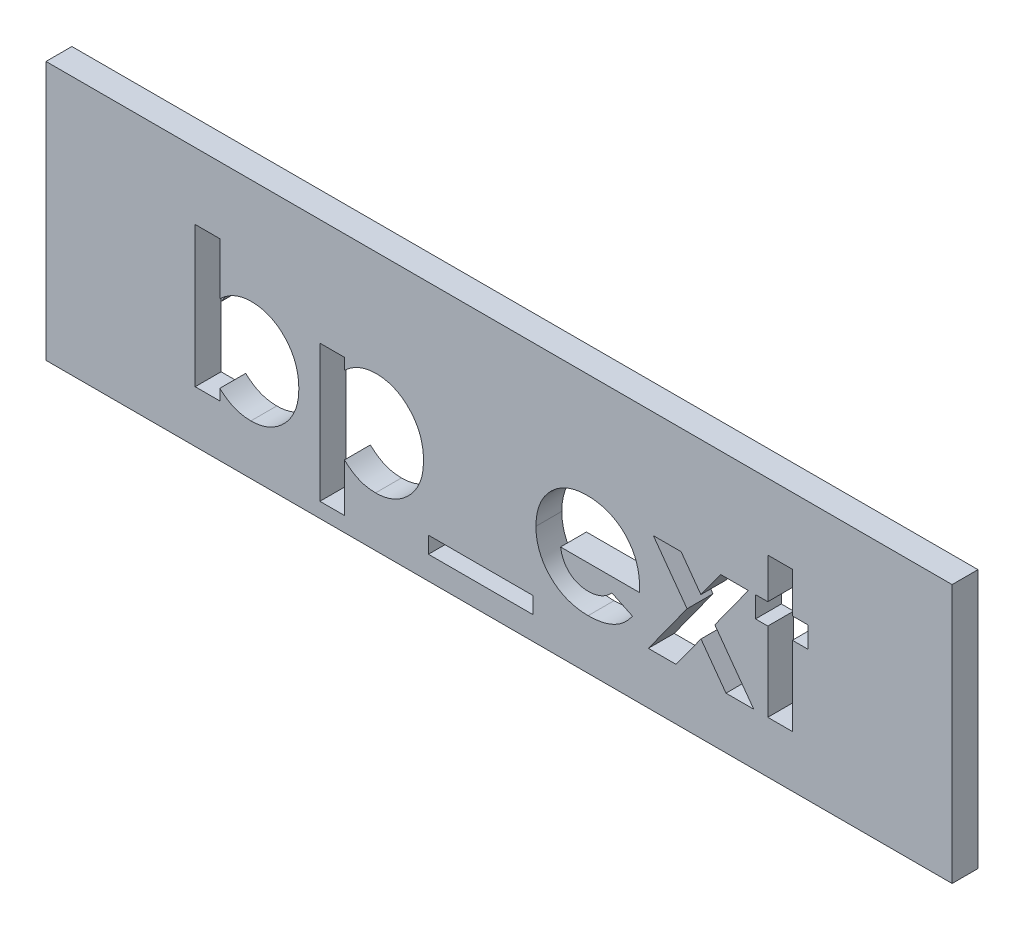
SolidWorks part; units mm, degrees
ref_plane "Plan de face" through (0, 0, 0) normal (0, 0, 1) x (1, 0, 0)
ref_plane "Plan de dessus" through (0, 0, 0) normal (0, 1, 0) x (1, 0, 0)
ref_plane "Plan de droite" through (0, 0, 0) normal (1, 0, 0) x (0, 0, -1)
sketch "Esquisse1" plane through (0, 0, 0) normal (0, 0, 1) x (1, 0, 0)
  line L1 (0, 0) -> (35, 0)
  line L2 (0, 0) -> (0, -10)
  line L3 (0, -10) -> (35, -10)
  line L4 (35, 0) -> (35, -10)
  dimension "D1" = 35
  dimension "D2" = 10
extrude "Boss.-Extru.1" add sketch "Esquisse1" along normal blind 1
sketch "Esquisse2" plane through (0, 0, 0) normal (0, 0, -1) x (-1, 0, 0)
  line L0 (-35, 0) -> (0, 0) construction
  line L1 (-35, -10) -> (-35, 0) construction
  line L2 (0, 0) -> (0, -10) construction
  circle A0 centre (-30, -5) radius 1
  circle A1 centre (-5, -5) radius 1
  dimension "D4" = 2
  dimension "D1" = 5
  dimension "D2" = 5
  dimension "D3" = 5
extrude "Boss.-Extru.2" add sketch "Esquisse2" along normal blind 3
chamfer "Chanfrein1" distance 0.5 angle 45 2 edges at (29, -5, -3) (4, -5, -3)
sketch "Esquisse3" plane through (0, 0, 1) normal (0, 0, 1) x (1, 0, 0)
  line L0 (5, -8) -> (30, -8) construction
  line L3 (0, -10) -> (35, -10) construction
  line L4 (0, 0) -> (0, -10) construction
  line L5 (35, -10) -> (35, 0) construction
  text T1 "<b>bp_ext</b>" font "Century Gothic" height in points 20
  point P12 (30, -8)
  dimension "D1" = 2
  dimension "D2" = 5
  dimension "D3" = 25
  dimension "D4" = 5
extrude "Enlèv. mat.-Extru.2" cut sketch "Esquisse3" against normal blind 1
sketch "Esquisse4" plane through (0, 0, 1) normal (0, 0, 1) x (1, 0, 0)
  line L8 (14.772, -9.0998) -> (18.8033, -9.0998)
  line L9 (14.772, -8.4606) -> (14.772, -9.0998)
  line L10 (18.8033, -8.4606) -> (14.772, -8.4606)
  line L11 (18.8033, -9.0998) -> (18.8033, -8.4606)
  line L12 (14.772, -9.0998) -> (18.8033, -9.0998)
  line L13 (14.772, -8.4606) -> (14.772, -9.0998)
  line L14 (18.8033, -8.4606) -> (14.772, -8.4606)
  line L15 (18.8033, -9.0998) -> (18.8033, -8.4606)
  dimension "D1" = 0.15
extrude "Enlèv. mat.-Extru.3" cut sketch "Esquisse4" against normal through all
